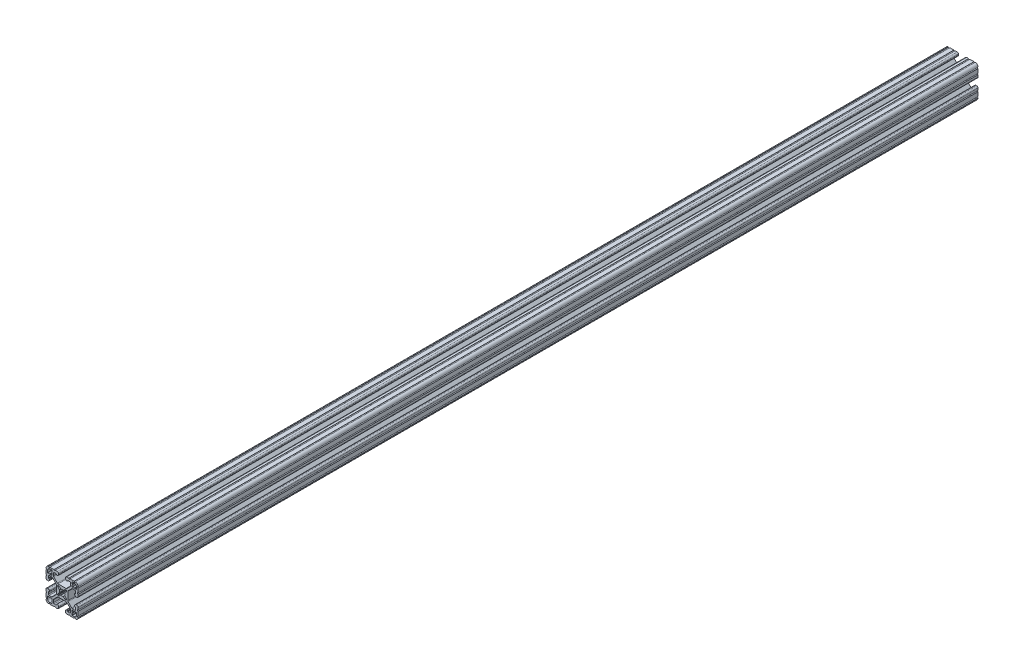
SolidWorks part; units mm, degrees
ref_plane "Front Plane" through (0, 0, 0) normal (0, 0, 1) x (1, 0, 0)
ref_plane "Top Plane" through (0, 0, 0) normal (0, 1, 0) x (1, 0, 0)
ref_plane "Right Plane" through (0, 0, 0) normal (1, 0, 0) x (0, 0, -1)
ref_plane "Plane1" through (0, 0, -2322.576) normal (0, 0, -1) x (-1, 0, 0)
sketch "Sketch1" plane through (0, 0, -2322.576) normal (0, 0, -1) x (-1, 0, 0)
  line L0 (17.2466, 14.4526) -> (17.2466, 12.2428)
  line L1 (16.8656, 11.8618) -> (15.0927, 11.8618)
  line L2 (15.0927, 11.8618) -> (14.5542, 12.4003)
  line L3 (14.5542, 12.4003) -> (14.0157, 11.8618)
  line L4 (14.0157, 11.8618) -> (12.2428, 11.8618)
  line L5 (11.8618, 12.2428) -> (11.8618, 14.0157)
  line L6 (11.8618, 14.0157) -> (12.4003, 14.5542)
  line L7 (12.4003, 14.5542) -> (11.8618, 15.0927)
  line L8 (11.8618, 15.0927) -> (11.8618, 16.8656)
  line L9 (12.2428, 17.2466) -> (14.4526, 17.2466)
  line L10 (17.2466, -12.2428) -> (17.2466, -14.4526)
  line L11 (14.4526, -17.2466) -> (12.2428, -17.2466)
  line L12 (11.8618, -16.8656) -> (11.8618, -15.0927)
  line L13 (11.8618, -15.0927) -> (12.4003, -14.5542)
  line L14 (12.4003, -14.5542) -> (11.8618, -14.0157)
  line L15 (11.8618, -14.0157) -> (11.8618, -12.2428)
  line L16 (12.2428, -11.8618) -> (14.0157, -11.8618)
  line L17 (14.0157, -11.8618) -> (14.5542, -12.4003)
  line L18 (14.5542, -12.4003) -> (15.0927, -11.8618)
  line L19 (15.0927, -11.8618) -> (16.8656, -11.8618)
  line L20 (5.1689, -3.9207) -> (5.1689, -4.9149)
  line L21 (4.9149, -5.1689) -> (3.9207, -5.1689)
  line L22 (3.2921, -4.9085) -> (1.5823, -3.1988)
  line L23 (-1.5823, -3.1988) -> (-3.2921, -4.9085)
  line L24 (-3.9207, -5.1689) -> (-4.9149, -5.1689)
  line L25 (-5.1689, -4.9149) -> (-5.1689, -3.9207)
  line L26 (-4.9085, -3.2921) -> (-3.1988, -1.5823)
  line L27 (-3.1988, 1.5823) -> (-4.9085, 3.2921)
  line L28 (-5.1689, 3.9207) -> (-5.1689, 4.9149)
  line L29 (-4.9149, 5.1689) -> (-3.9207, 5.1689)
  line L30 (-3.2921, 4.9085) -> (-1.5823, 3.1988)
  line L31 (1.5823, 3.1988) -> (3.2921, 4.9085)
  line L32 (3.9207, 5.1689) -> (4.9149, 5.1689)
  line L33 (5.1689, 4.9149) -> (5.1689, 3.9207)
  line L34 (4.9085, 3.2921) -> (3.1988, 1.5823)
  line L35 (3.1988, -1.5823) -> (4.9085, -3.2921)
  line L36 (-11.8618, -12.2428) -> (-11.8618, -14.0157)
  line L37 (-11.8618, -14.0157) -> (-12.4003, -14.5542)
  line L38 (-12.4003, -14.5542) -> (-11.8618, -15.0927)
  line L39 (-11.8618, -15.0927) -> (-11.8618, -16.8656)
  line L40 (-12.2428, -17.2466) -> (-14.4526, -17.2466)
  line L41 (-17.2466, -14.4526) -> (-17.2466, -12.2428)
  line L42 (-16.8656, -11.8618) -> (-15.0927, -11.8618)
  line L43 (-15.0927, -11.8618) -> (-14.5542, -12.4003)
  line L44 (-14.5542, -12.4003) -> (-14.0157, -11.8618)
  line L45 (-14.0157, -11.8618) -> (-12.2428, -11.8618)
  line L46 (-11.8618, 16.8656) -> (-11.8618, 15.0927)
  line L47 (-11.8618, 15.0927) -> (-12.4003, 14.5542)
  line L48 (-12.4003, 14.5542) -> (-11.8618, 14.0157)
  line L49 (-11.8618, 14.0157) -> (-11.8618, 12.2428)
  line L50 (-12.2428, 11.8618) -> (-14.0157, 11.8618)
  line L51 (-14.0157, 11.8618) -> (-14.5542, 12.4003)
  line L52 (-14.5542, 12.4003) -> (-15.0927, 11.8618)
  line L53 (-15.0927, 11.8618) -> (-16.8656, 11.8618)
  line L54 (-17.2466, 12.2428) -> (-17.2466, 14.4526)
  line L55 (-14.4526, 17.2466) -> (-12.2428, 17.2466)
  line L56 (19.05, -14.3256) -> (19.05, -9.4996)
  line L57 (19.05, -7.9756) -> (19.05, -5.6388)
  line L58 (17.4752, -4.064) -> (16.5608, -4.064)
  line L59 (14.986, -5.6388) -> (14.986, -6.35)
  line L60 (15.367, -6.731) -> (15.6972, -6.731)
  line L61 (16.0782, -7.112) -> (16.0782, -9.398)
  line L62 (15.1892, -10.287) -> (12.3756, -10.287)
  line L63 (11.4776, -9.915) -> (7.1157, -5.5531)
  line L64 (6.7437, -4.6551) -> (6.7437, 4.6551)
  line L65 (7.1157, 5.5531) -> (11.4776, 9.915)
  line L66 (12.3756, 10.287) -> (15.1892, 10.287)
  line L67 (16.0782, 9.398) -> (16.0782, 7.112)
  line L68 (15.6972, 6.731) -> (15.367, 6.731)
  line L69 (14.986, 6.35) -> (14.986, 5.6388)
  line L70 (16.5608, 4.064) -> (17.4752, 4.064)
  line L71 (19.05, 5.6388) -> (19.05, 7.9756)
  line L72 (19.05, 9.4996) -> (19.05, 14.3256)
  line L73 (14.3256, 19.05) -> (9.4996, 19.05)
  line L74 (7.9756, 19.05) -> (5.6388, 19.05)
  line L75 (4.064, 17.4752) -> (4.064, 16.5608)
  line L76 (5.6388, 14.986) -> (6.35, 14.986)
  line L77 (6.731, 15.367) -> (6.731, 15.6972)
  line L78 (7.112, 16.0782) -> (9.398, 16.0782)
  line L79 (10.287, 15.1892) -> (10.287, 12.3756)
  line L80 (9.915, 11.4776) -> (5.5531, 7.1157)
  line L81 (4.6551, 6.7437) -> (-4.6551, 6.7437)
  line L82 (-5.5531, 7.1157) -> (-9.915, 11.4776)
  line L83 (-10.287, 12.3756) -> (-10.287, 15.1892)
  line L84 (-9.398, 16.0782) -> (-7.112, 16.0782)
  line L85 (-6.731, 15.6972) -> (-6.731, 15.367)
  line L86 (-6.35, 14.986) -> (-5.6388, 14.986)
  line L87 (-4.064, 16.5608) -> (-4.064, 17.4752)
  line L88 (-5.6388, 19.05) -> (-7.9756, 19.05)
  line L89 (-9.4996, 19.05) -> (-14.3256, 19.05)
  line L90 (-19.05, 14.3256) -> (-19.05, 9.4996)
  line L91 (-19.05, 7.9756) -> (-19.05, 5.6388)
  line L92 (-17.4752, 4.064) -> (-16.5608, 4.064)
  line L93 (-14.986, 5.6388) -> (-14.986, 6.35)
  line L94 (-15.367, 6.731) -> (-15.6972, 6.731)
  line L95 (-16.0782, 7.112) -> (-16.0782, 9.398)
  line L96 (-15.1892, 10.287) -> (-12.3756, 10.287)
  line L97 (-11.4776, 9.915) -> (-7.1157, 5.5531)
  line L98 (-6.7437, 4.6551) -> (-6.7437, -4.6551)
  line L99 (-7.1157, -5.5531) -> (-11.4776, -9.915)
  line L100 (-12.3756, -10.287) -> (-15.1892, -10.287)
  line L101 (-16.0782, -9.398) -> (-16.0782, -7.112)
  line L102 (-15.6972, -6.731) -> (-15.367, -6.731)
  line L103 (-14.986, -6.35) -> (-14.986, -5.6388)
  line L104 (-16.5608, -4.064) -> (-17.4752, -4.064)
  line L105 (-19.05, -5.6388) -> (-19.05, -7.9756)
  line L106 (-19.05, -9.4996) -> (-19.05, -14.3256)
  line L107 (-14.3256, -19.05) -> (-9.4996, -19.05)
  line L108 (-7.9756, -19.05) -> (-5.6388, -19.05)
  line L109 (-4.064, -17.4752) -> (-4.064, -16.5608)
  line L110 (-5.6388, -14.986) -> (-6.35, -14.986)
  line L111 (-6.731, -15.367) -> (-6.731, -15.6972)
  line L112 (-7.112, -16.0782) -> (-9.398, -16.0782)
  line L113 (-10.287, -15.1892) -> (-10.287, -12.3756)
  line L114 (-9.915, -11.4776) -> (-5.5531, -7.1157)
  line L115 (-4.6551, -6.7437) -> (4.6551, -6.7437)
  line L116 (5.5531, -7.1157) -> (9.915, -11.4776)
  line L117 (10.287, -12.3756) -> (10.287, -15.1892)
  line L118 (9.398, -16.0782) -> (7.112, -16.0782)
  line L119 (6.731, -15.6972) -> (6.731, -15.367)
  line L120 (6.35, -14.986) -> (5.6388, -14.986)
  line L121 (4.064, -16.5608) -> (4.064, -17.4752)
  line L122 (5.6388, -19.05) -> (7.9756, -19.05)
  line L123 (9.4996, -19.05) -> (14.3256, -19.05)
  arc A0 (17.2466, 12.2428) -> (16.8656, 11.8618) centre (16.8656, 12.2428) cw
  arc A1 (12.2428, 11.8618) -> (11.8618, 12.2428) centre (12.2428, 12.2428) cw
  arc A2 (11.8618, 16.8656) -> (12.2428, 17.2466) centre (12.2428, 16.8656) cw
  arc A3 (14.4526, 17.2466) -> (17.2466, 14.4526) centre (14.4526, 14.4526) cw
  arc A4 (17.2466, -14.4526) -> (14.4526, -17.2466) centre (14.4526, -14.4526) cw
  arc A5 (12.2428, -17.2466) -> (11.8618, -16.8656) centre (12.2428, -16.8656) cw
  arc A6 (11.8618, -12.2428) -> (12.2428, -11.8618) centre (12.2428, -12.2428) cw
  arc A7 (16.8656, -11.8618) -> (17.2466, -12.2428) centre (16.8656, -12.2428) cw
  arc A8 (5.1689, -4.9149) -> (4.9149, -5.1689) centre (4.9149, -4.9149) cw
  arc A9 (3.9207, -5.1689) -> (3.2921, -4.9085) centre (3.9207, -4.2799) cw
  arc A10 (1.5823, -3.1988) -> (1.178, -3.1119) centre (1.3129, -3.4682) ccw
  arc A11 (1.178, -3.1119) -> (-1.178, -3.1119) centre (0, 0) cw
  arc A12 (-1.178, -3.1119) -> (-1.5823, -3.1988) centre (-1.3129, -3.4682) ccw
  arc A13 (-3.2921, -4.9085) -> (-3.9207, -5.1689) centre (-3.9207, -4.2799) cw
  arc A14 (-4.9149, -5.1689) -> (-5.1689, -4.9149) centre (-4.9149, -4.9149) cw
  arc A15 (-5.1689, -3.9207) -> (-4.9085, -3.2921) centre (-4.2799, -3.9207) cw
  arc A16 (-3.1988, -1.5823) -> (-3.1119, -1.178) centre (-3.4682, -1.3129) ccw
  arc A17 (-3.1119, -1.178) -> (-3.1119, 1.178) centre (0, 0) cw
  arc A18 (-3.1119, 1.178) -> (-3.1988, 1.5823) centre (-3.4682, 1.3129) ccw
  arc A19 (-4.9085, 3.2921) -> (-5.1689, 3.9207) centre (-4.2799, 3.9207) cw
  arc A20 (-5.1689, 4.9149) -> (-4.9149, 5.1689) centre (-4.9149, 4.9149) cw
  arc A21 (-3.9207, 5.1689) -> (-3.2921, 4.9085) centre (-3.9207, 4.2799) cw
  arc A22 (-1.5823, 3.1988) -> (-1.178, 3.1119) centre (-1.3129, 3.4682) ccw
  arc A23 (-1.178, 3.1119) -> (1.178, 3.1119) centre (0, 0) cw
  arc A24 (1.178, 3.1119) -> (1.5823, 3.1988) centre (1.3129, 3.4682) ccw
  arc A25 (3.2921, 4.9085) -> (3.9207, 5.1689) centre (3.9207, 4.2799) cw
  arc A26 (4.9149, 5.1689) -> (5.1689, 4.9149) centre (4.9149, 4.9149) cw
  arc A27 (5.1689, 3.9207) -> (4.9085, 3.2921) centre (4.2799, 3.9207) cw
  arc A28 (3.1988, 1.5823) -> (3.1119, 1.178) centre (3.4682, 1.3129) ccw
  arc A29 (3.1119, 1.178) -> (3.1119, -1.178) centre (0, 0) cw
  arc A30 (3.1119, -1.178) -> (3.1988, -1.5823) centre (3.4682, -1.3129) ccw
  arc A31 (4.9085, -3.2921) -> (5.1689, -3.9207) centre (4.2799, -3.9207) cw
  arc A32 (-11.8618, -16.8656) -> (-12.2428, -17.2466) centre (-12.2428, -16.8656) cw
  arc A33 (-14.4526, -17.2466) -> (-17.2466, -14.4526) centre (-14.4526, -14.4526) cw
  arc A34 (-17.2466, -12.2428) -> (-16.8656, -11.8618) centre (-16.8656, -12.2428) cw
  arc A35 (-12.2428, -11.8618) -> (-11.8618, -12.2428) centre (-12.2428, -12.2428) cw
  arc A36 (-12.2428, 17.2466) -> (-11.8618, 16.8656) centre (-12.2428, 16.8656) cw
  arc A37 (-11.8618, 12.2428) -> (-12.2428, 11.8618) centre (-12.2428, 12.2428) cw
  arc A38 (-16.8656, 11.8618) -> (-17.2466, 12.2428) centre (-16.8656, 12.2428) cw
  arc A39 (-17.2466, 14.4526) -> (-14.4526, 17.2466) centre (-14.4526, 14.4526) cw
  arc A40 (19.05, -9.4996) -> (19.05, -7.9756) centre (19.05, -8.7376) cw
  arc A41 (19.05, -5.6388) -> (17.4752, -4.064) centre (17.4752, -5.6388) ccw
  arc A42 (16.5608, -4.064) -> (14.986, -5.6388) centre (16.5608, -5.6388) ccw
  arc A43 (14.986, -6.35) -> (15.367, -6.731) centre (15.367, -6.35) ccw
  arc A44 (15.6972, -6.731) -> (16.0782, -7.112) centre (15.6972, -7.112) cw
  arc A45 (16.0782, -9.398) -> (15.1892, -10.287) centre (15.1892, -9.398) cw
  arc A46 (12.3756, -10.287) -> (11.4776, -9.915) centre (12.3756, -9.017) cw
  arc A47 (7.1157, -5.5531) -> (6.7437, -4.6551) centre (8.0137, -4.6551) cw
  arc A48 (6.7437, 4.6551) -> (7.1157, 5.5531) centre (8.0137, 4.6551) cw
  arc A49 (11.4776, 9.915) -> (12.3756, 10.287) centre (12.3756, 9.017) cw
  arc A50 (15.1892, 10.287) -> (16.0782, 9.398) centre (15.1892, 9.398) cw
  arc A51 (16.0782, 7.112) -> (15.6972, 6.731) centre (15.6972, 7.112) cw
  arc A52 (15.367, 6.731) -> (14.986, 6.35) centre (15.367, 6.35) ccw
  arc A53 (14.986, 5.6388) -> (16.5608, 4.064) centre (16.5608, 5.6388) ccw
  arc A54 (17.4752, 4.064) -> (19.05, 5.6388) centre (17.4752, 5.6388) ccw
  arc A55 (19.05, 7.9756) -> (19.05, 9.4996) centre (19.05, 8.7376) cw
  arc A56 (19.05, 14.3256) -> (19.0499, 15.8496) centre (19.05, 15.0876) cw
  arc A57 (19.0499, 15.8496) -> (15.8496, 19.0499) centre (15.875, 15.875) ccw
  arc A58 (15.8496, 19.0499) -> (14.3256, 19.05) centre (15.0876, 19.05) cw
  arc A59 (9.4996, 19.05) -> (7.9756, 19.05) centre (8.7376, 19.05) cw
  arc A60 (5.6388, 19.05) -> (4.064, 17.4752) centre (5.6388, 17.4752) ccw
  arc A61 (4.064, 16.5608) -> (5.6388, 14.986) centre (5.6388, 16.5608) ccw
  arc A62 (6.35, 14.986) -> (6.731, 15.367) centre (6.35, 15.367) ccw
  arc A63 (6.731, 15.6972) -> (7.112, 16.0782) centre (7.112, 15.6972) cw
  arc A64 (9.398, 16.0782) -> (10.287, 15.1892) centre (9.398, 15.1892) cw
  arc A65 (10.287, 12.3756) -> (9.915, 11.4776) centre (9.017, 12.3756) cw
  arc A66 (5.5531, 7.1157) -> (4.6551, 6.7437) centre (4.6551, 8.0137) cw
  arc A67 (-4.6551, 6.7437) -> (-5.5531, 7.1157) centre (-4.6551, 8.0137) cw
  arc A68 (-9.915, 11.4776) -> (-10.287, 12.3756) centre (-9.017, 12.3756) cw
  arc A69 (-10.287, 15.1892) -> (-9.398, 16.0782) centre (-9.398, 15.1892) cw
  arc A70 (-7.112, 16.0782) -> (-6.731, 15.6972) centre (-7.112, 15.6972) cw
  arc A71 (-6.731, 15.367) -> (-6.35, 14.986) centre (-6.35, 15.367) ccw
  arc A72 (-5.6388, 14.986) -> (-4.064, 16.5608) centre (-5.6388, 16.5608) ccw
  arc A73 (-4.064, 17.4752) -> (-5.6388, 19.05) centre (-5.6388, 17.4752) ccw
  arc A74 (-7.9756, 19.05) -> (-9.4996, 19.05) centre (-8.7376, 19.05) cw
  arc A75 (-14.3256, 19.05) -> (-15.8496, 19.0499) centre (-15.0876, 19.05) cw
  arc A76 (-15.8496, 19.0499) -> (-19.0499, 15.8496) centre (-15.875, 15.875) ccw
  arc A77 (-19.0499, 15.8496) -> (-19.05, 14.3256) centre (-19.05, 15.0876) cw
  arc A78 (-19.05, 9.4996) -> (-19.05, 7.9756) centre (-19.05, 8.7376) cw
  arc A79 (-19.05, 5.6388) -> (-17.4752, 4.064) centre (-17.4752, 5.6388) ccw
  arc A80 (-16.5608, 4.064) -> (-14.986, 5.6388) centre (-16.5608, 5.6388) ccw
  arc A81 (-14.986, 6.35) -> (-15.367, 6.731) centre (-15.367, 6.35) ccw
  arc A82 (-15.6972, 6.731) -> (-16.0782, 7.112) centre (-15.6972, 7.112) cw
  arc A83 (-16.0782, 9.398) -> (-15.1892, 10.287) centre (-15.1892, 9.398) cw
  arc A84 (-12.3756, 10.287) -> (-11.4776, 9.915) centre (-12.3756, 9.017) cw
  arc A85 (-7.1157, 5.5531) -> (-6.7437, 4.6551) centre (-8.0137, 4.6551) cw
  arc A86 (-6.7437, -4.6551) -> (-7.1157, -5.5531) centre (-8.0137, -4.6551) cw
  arc A87 (-11.4776, -9.915) -> (-12.3756, -10.287) centre (-12.3756, -9.017) cw
  arc A88 (-15.1892, -10.287) -> (-16.0782, -9.398) centre (-15.1892, -9.398) cw
  arc A89 (-16.0782, -7.112) -> (-15.6972, -6.731) centre (-15.6972, -7.112) cw
  arc A90 (-15.367, -6.731) -> (-14.986, -6.35) centre (-15.367, -6.35) ccw
  arc A91 (-14.986, -5.6388) -> (-16.5608, -4.064) centre (-16.5608, -5.6388) ccw
  arc A92 (-17.4752, -4.064) -> (-19.05, -5.6388) centre (-17.4752, -5.6388) ccw
  arc A93 (-19.05, -7.9756) -> (-19.05, -9.4996) centre (-19.05, -8.7376) cw
  arc A94 (-19.05, -14.3256) -> (-19.0499, -15.8496) centre (-19.05, -15.0876) cw
  arc A95 (-19.0499, -15.8496) -> (-15.8496, -19.0499) centre (-15.875, -15.875) ccw
  arc A96 (-15.8496, -19.0499) -> (-14.3256, -19.05) centre (-15.0876, -19.05) cw
  arc A97 (-9.4996, -19.05) -> (-7.9756, -19.05) centre (-8.7376, -19.05) cw
  arc A98 (-5.6388, -19.05) -> (-4.064, -17.4752) centre (-5.6388, -17.4752) ccw
  arc A99 (-4.064, -16.5608) -> (-5.6388, -14.986) centre (-5.6388, -16.5608) ccw
  arc A100 (-6.35, -14.986) -> (-6.731, -15.367) centre (-6.35, -15.367) ccw
  arc A101 (-6.731, -15.6972) -> (-7.112, -16.0782) centre (-7.112, -15.6972) cw
  arc A102 (-9.398, -16.0782) -> (-10.287, -15.1892) centre (-9.398, -15.1892) cw
  arc A103 (-10.287, -12.3756) -> (-9.915, -11.4776) centre (-9.017, -12.3756) cw
  arc A104 (-5.5531, -7.1157) -> (-4.6551, -6.7437) centre (-4.6551, -8.0137) cw
  arc A105 (4.6551, -6.7437) -> (5.5531, -7.1157) centre (4.6551, -8.0137) cw
  arc A106 (9.915, -11.4776) -> (10.287, -12.3756) centre (9.017, -12.3756) cw
  arc A107 (10.287, -15.1892) -> (9.398, -16.0782) centre (9.398, -15.1892) cw
  arc A108 (7.112, -16.0782) -> (6.731, -15.6972) centre (7.112, -15.6972) cw
  arc A109 (6.731, -15.367) -> (6.35, -14.986) centre (6.35, -15.367) ccw
  arc A110 (5.6388, -14.986) -> (4.064, -16.5608) centre (5.6388, -16.5608) ccw
  arc A111 (4.064, -17.4752) -> (5.6388, -19.05) centre (5.6388, -17.4752) ccw
  arc A112 (7.9756, -19.05) -> (9.4996, -19.05) centre (8.7376, -19.05) cw
  arc A113 (14.3256, -19.05) -> (15.8496, -19.0499) centre (15.0876, -19.05) cw
  arc A114 (15.8496, -19.0499) -> (19.0499, -15.8496) centre (15.875, -15.875) ccw
  arc A115 (19.0499, -15.8496) -> (19.05, -14.3256) centre (19.05, -15.0876) cw
extrude "Boss-Extrude1" add sketch "Sketch1" against normal blind 1066.8
